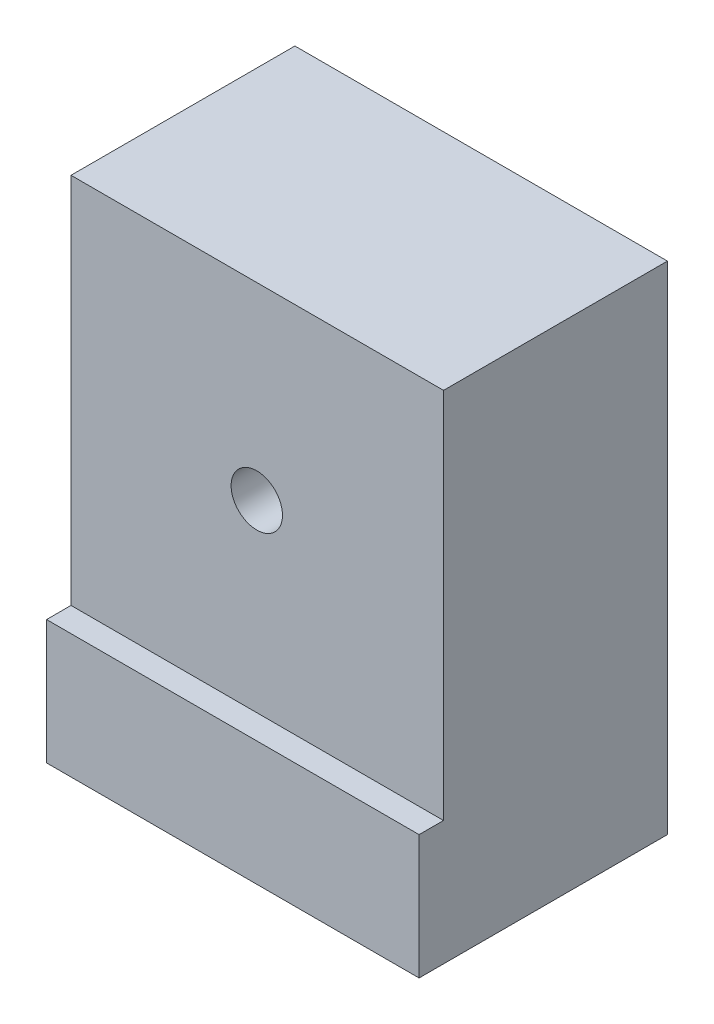
SolidWorks part; units mm, degrees
ref_plane "Front Plane" through (0, 0, 0) normal (0, 0, 1) x (1, 0, 0)
ref_plane "Top Plane" through (0, 0, 0) normal (0, 1, 0) x (1, 0, 0)
ref_plane "Right Plane" through (0, 0, 0) normal (1, 0, 0) x (0, 0, -1)
sketch "Sketch1" plane through (0, 0, 0) normal (0, 1, 0) x (1, 0, 0)
  line L1 (0, 0) -> (76.2, 0)
  line L2 (0, 0) -> (0, 50.8)
  line L3 (0, 50.8) -> (76.2, 50.8)
  line L4 (76.2, 0) -> (76.2, 50.8)
  dimension "D1" = 76.2
  dimension "D2" = 50.8
extrude "Boss-Extrude1" add sketch "Sketch1" along normal blind 101.6
sketch "Sketch2" plane through (0, 0, 0) normal (0, 0, 1) x (1, 0, 0)
  line L1 (0, 0) -> (38, 0)
  line L2 (0, 0) -> (0, 63)
  line L3 (0, 63) -> (38, 63)
  line L4 (38, 0) -> (38, 63)
  circle A0 centre (38, 63) radius 5.25
  dimension "D1" = 38
  dimension "D2" = 63
extrude "Cut-Extrude1" cut sketch "Sketch2" against normal blind 300 contours A0
sketch "Sketch3" plane through (0, 0, 0) normal (0, 0, 1) x (1, 0, 0)
  line L0 (76.2, 101.6) -> (76.2, 0) construction
  line L1 (0, 101.6) -> (76.2, 101.6)
  line L2 (0, 101.6) -> (0, 25.4)
  line L3 (0, 25.4) -> (76.2, 25.4)
  line L4 (76.2, 101.6) -> (76.2, 25.4)
  dimension "D1" = 76.2
extrude "Cut-Extrude2" cut sketch "Sketch3" against normal blind 5
